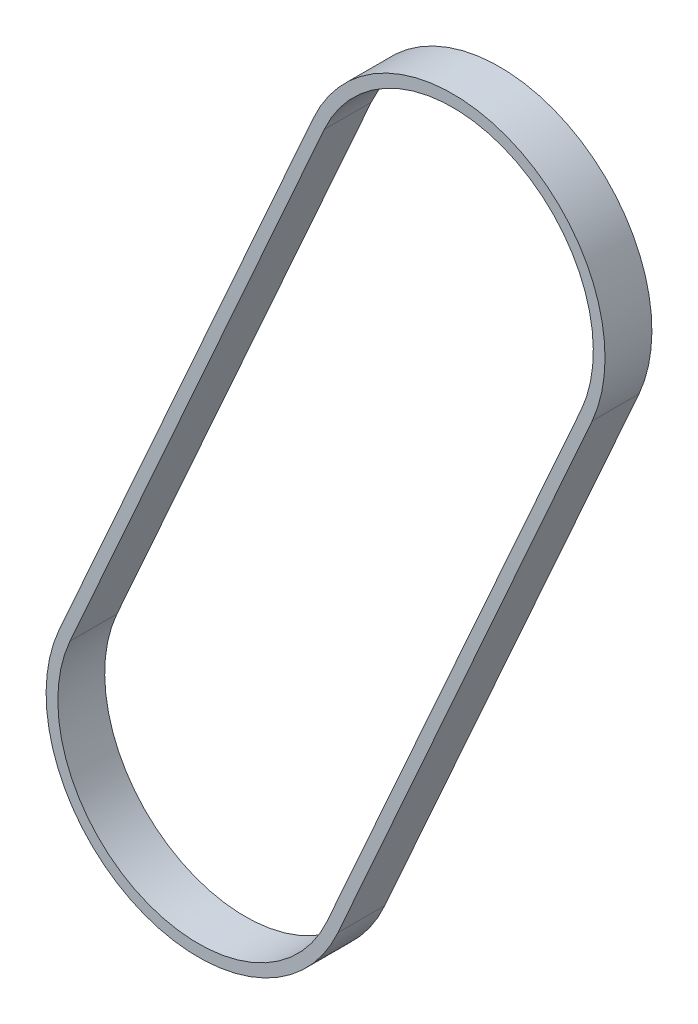
SolidWorks part; units mm, degrees
ref_plane "前视基准面" through (0, 0, 0) normal (0, 0, 1) x (1, 0, 0)
ref_plane "上视基准面" through (0, 0, 0) normal (0, 1, 0) x (1, 0, 0)
ref_plane "右视基准面" through (0, 0, 0) normal (1, 0, 0) x (0, 0, -1)
other "Configuration Table"
sketch "草图1" plane through (0, 0, 0) normal (0, 0, 1) x (1, 0, 0)
  line L0 (0, 0) -> (54.2476, 121.6663)
  line L1 (27.3998, -12.2168) -> (-27.3998, 12.2168)
  line L2 (81.6474, 109.4495) -> (26.8478, 133.8832)
  line L3 (26.8478, 133.8832) -> (-27.3998, 12.2168)
  line L4 (81.6474, 109.4495) -> (27.3998, -12.2168)
  line L5 (83.9995, 108.5868) -> (24.4957, 134.7459)
  line L6 (29.7519, -13.0796) -> (-29.7519, 13.0796)
  line L7 (24.4957, 134.7459) -> (-29.7519, 13.0796)
  line L8 (83.9995, 108.5868) -> (29.7519, -13.0796)
  arc A0 (-27.3998, 12.2168) -> (27.3998, -12.2168) centre (0, 0) ccw
  arc A1 (26.8478, 133.8832) -> (81.6474, 109.4495) centre (54.2476, 121.6663) cw
  arc A2 (83.9995, 108.5868) -> (24.4957, 134.7459) centre (54.2476, 121.6663) ccw
  arc A3 (-29.7519, 13.0796) -> (29.7519, -13.0796) centre (0, 0) ccw
  point P8 (0, 0)
  point P11 (54.2476, 121.6663)
  point P14 (54.2476, 121.6663)
  point P17 (0, 0)
  dimension "D1" = 65
  dimension "D2" = 60
  dimension "D3" = 60
  dimension "D4" = 65
extrude "凸台-拉伸1" add sketch "草图1" along normal blind 10 contours L5 A2 L3 A1 | A0 L3 L5 L7 L6 | L5 A1 L4 L6 L8 | L6 A3 L4 A0
